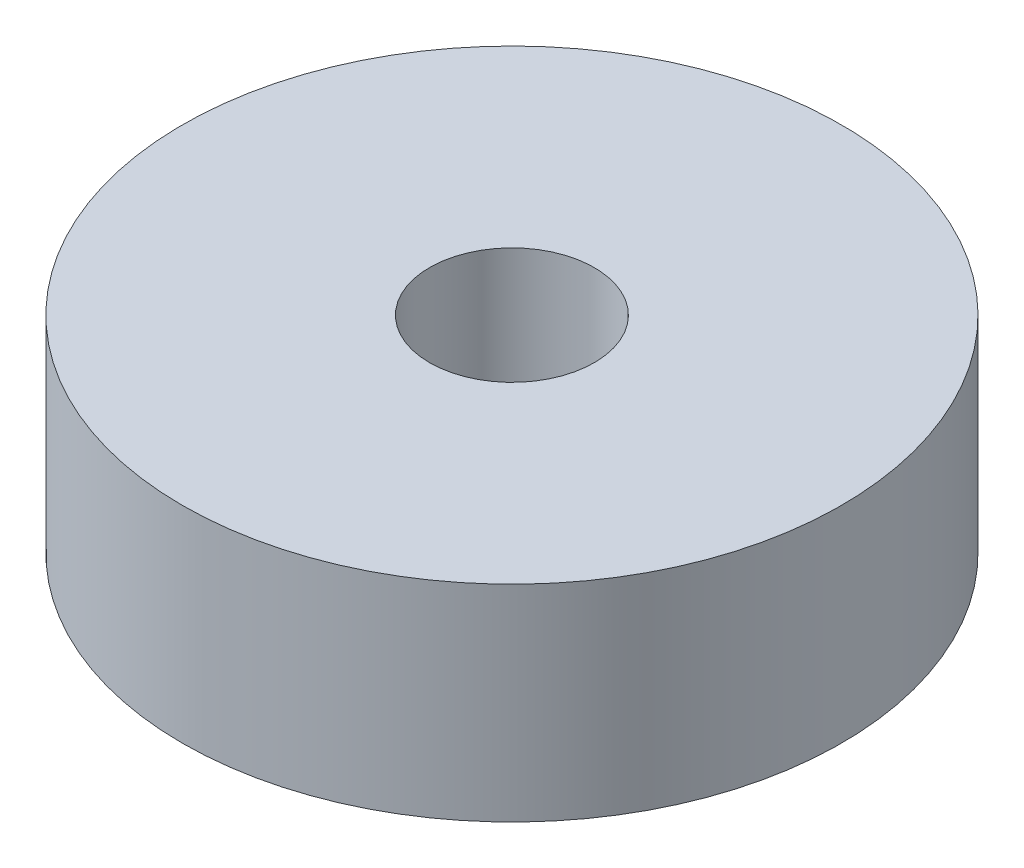
SolidWorks part; units mm, degrees
material "不锈钢 (铁素体)"
ref_plane "前视基准面" through (0, 0, 0) normal (0, 0, 1) x (1, 0, 0)
ref_plane "上视基准面" through (0, 0, 0) normal (0, 1, 0) x (1, 0, 0)
ref_plane "右视基准面" through (0, 0, 0) normal (1, 0, 0) x (0, 0, -1)
sketch "草图1" plane through (0, 0, 0) normal (0, 1, 0) x (1, 0, 0)
  circle A0 centre (0, 0) radius 2
  circle A1 centre (0, 0) radius 8
  dimension "D1" = 4
  dimension "D2" = 16
extrude "凸台-拉伸1" add sketch "草图1" along normal blind 5
